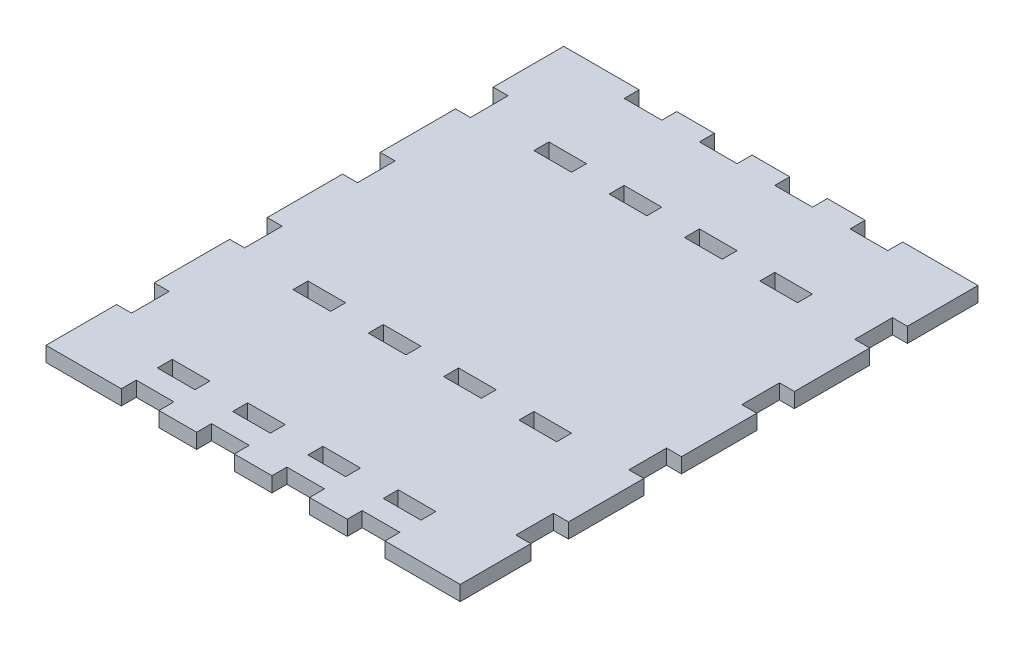
SolidWorks part; units mm, degrees
ref_plane "Front Plane" through (0, 0, 0) normal (0, 0, 1) x (1, 0, 0)
ref_plane "Top Plane" through (0, 0, 0) normal (0, 1, 0) x (1, 0, 0)
ref_plane "Right Plane" through (0, 0, 0) normal (1, 0, 0) x (0, 0, -1)
sketch "Sketch1" plane through (0, 0, 0) normal (0, 1, 0) x (1, 0, 0)
  line L1 (0, 0) -> (88, 0)
  line L2 (0, 0) -> (0, -110)
  line L3 (0, -110) -> (88, -110)
  line L4 (88, 0) -> (88, -110)
  dimension "D1" = 110
  dimension "D2" = 88
extrude "Boss-Extrude1" add sketch "Sketch1" along normal blind 3.175
sketch "Sketch2" plane through (0, 3.175, 0) normal (0, 1, 0) x (1, 0, 0)
  line L0 (44, 0) -> (44, -110) construction
  line L1 (88, 0) -> (0, 0) construction
  line L2 (0, -110) -> (88, -110) construction
  line L3 (64, 0) -> (64, -3.175)
  line L4 (48, 0) -> (56, 0)
  line L5 (48, 0) -> (48, -3.175)
  line L6 (48, -3.175) -> (56, -3.175)
  line L7 (56, 0) -> (56, -3.175)
  line L8 (64, 0) -> (72, 0)
  line L9 (64, -3.175) -> (72, -3.175)
  line L10 (72, 0) -> (72, -3.175)
  line L11 (16, 0) -> (16, -3.175)
  line L12 (24, -3.175) -> (16, -3.175)
  line L13 (24, 0) -> (16, 0)
  line L14 (32, 0) -> (32, -3.175)
  line L15 (40, -3.175) -> (32, -3.175)
  line L16 (40, 0) -> (40, -3.175)
  line L17 (40, 0) -> (32, 0)
  line L18 (24, 0) -> (24, -3.175)
  line L19 (88, -55) -> (0, -55) construction
  line L20 (88, -110) -> (88, 0) construction
  line L21 (0, 0) -> (0, -110) construction
  line L22 (0, -23) -> (3.175, -23)
  line L23 (0, -47) -> (3.175, -47)
  line L24 (0, -47) -> (0, -39)
  line L25 (0, -39) -> (3.175, -39)
  line L26 (3.175, -47) -> (3.175, -39)
  line L27 (0, -23) -> (0, -15)
  line L28 (0, -15) -> (3.175, -15)
  line L29 (3.175, -23) -> (3.175, -15)
  line L30 (3.175, -87) -> (3.175, -95)
  line L31 (0, -95) -> (3.175, -95)
  line L32 (0, -87) -> (0, -95)
  line L33 (3.175, -63) -> (3.175, -71)
  line L34 (0, -71) -> (3.175, -71)
  line L35 (0, -63) -> (0, -71)
  line L36 (0, -63) -> (3.175, -63)
  line L37 (0, -87) -> (3.175, -87)
  line L38 (24, -110) -> (24, -106.825)
  line L39 (40, -110) -> (32, -110)
  line L40 (40, -110) -> (40, -106.825)
  line L41 (40, -106.825) -> (32, -106.825)
  line L42 (32, -110) -> (32, -106.825)
  line L43 (24, -110) -> (16, -110)
  line L44 (24, -106.825) -> (16, -106.825)
  line L45 (16, -110) -> (16, -106.825)
  line L46 (72, -110) -> (72, -106.825)
  line L47 (64, -106.825) -> (72, -106.825)
  line L48 (64, -110) -> (72, -110)
  line L49 (56, -110) -> (56, -106.825)
  line L50 (48, -106.825) -> (56, -106.825)
  line L51 (48, -110) -> (48, -106.825)
  line L52 (48, -110) -> (56, -110)
  line L53 (64, -110) -> (64, -106.825)
  line L54 (88, -87) -> (84.825, -87)
  line L55 (88, -63) -> (84.825, -63)
  line L56 (88, -63) -> (88, -71)
  line L57 (88, -71) -> (84.825, -71)
  line L58 (84.825, -63) -> (84.825, -71)
  line L59 (88, -87) -> (88, -95)
  line L60 (88, -95) -> (84.825, -95)
  line L61 (84.825, -87) -> (84.825, -95)
  line L62 (84.825, -23) -> (84.825, -15)
  line L63 (88, -15) -> (84.825, -15)
  line L64 (88, -23) -> (88, -15)
  line L65 (84.825, -47) -> (84.825, -39)
  line L66 (88, -39) -> (84.825, -39)
  line L67 (88, -47) -> (88, -39)
  line L68 (88, -47) -> (84.825, -47)
  line L69 (88, -23) -> (84.825, -23)
  dimension "D1" = 8
  dimension "D2" = 4
  dimension "D4" = 3.175
  dimension "D5" = 3.175
  dimension "D6" = 8
  dimension "D7" = 8
  dimension "D3" = 2
  dimension "D8" = 2
extrude "Cut-Extrude1" cut sketch "Sketch2" against normal up to next
sketch "Sketch3" plane through (0, 3.175, 0) normal (0, 1, 0) x (1, 0, 0)
  line L0 (0, -19.175) -> (88, -19.175) construction
  line L1 (0, -23) -> (0, -39) construction
  line L2 (88, -39) -> (88, -23) construction
  line L3 (16, -3.175) -> (24, -3.175) construction
  line L4 (44, 0) -> (44, -110) construction
  line L5 (48, 0) -> (40, 0) construction
  line L6 (40, -110) -> (48, -110) construction
  line L7 (64, -19.175) -> (72, -19.175)
  line L8 (48, -19.175) -> (56, -19.175)
  line L9 (48, -19.175) -> (48, -22.35)
  line L10 (48, -22.35) -> (56, -22.35)
  line L11 (56, -19.175) -> (56, -22.35)
  line L12 (64, -19.175) -> (64, -22.35)
  line L13 (64, -22.35) -> (72, -22.35)
  line L14 (72, -19.175) -> (72, -22.35)
  line L15 (16, -19.175) -> (16, -22.35)
  line L16 (24, -22.35) -> (16, -22.35)
  line L17 (24, -19.175) -> (24, -22.35)
  line L18 (32, -19.175) -> (32, -22.35)
  line L19 (40, -22.35) -> (32, -22.35)
  line L20 (40, -19.175) -> (40, -22.35)
  line L21 (40, -19.175) -> (32, -19.175)
  line L22 (24, -19.175) -> (16, -19.175)
  dimension "D1" = 16
  dimension "D2" = 3.175
  dimension "D3" = 8
  dimension "D4" = 4
  dimension "D5" = 2
extrude "Cut-Extrude2" cut sketch "Sketch3" against normal up to next
sketch "Sketch4" plane through (0, 3.175, 0) normal (0, 1, 0) x (1, 0, 0)
  line L0 (0, -73.525) -> (88, -73.525) construction
  line L1 (0, -71) -> (0, -87) construction
  line L2 (88, -87) -> (88, -71) construction
  line L3 (64, -3.175) -> (72, -3.175) construction
  line L4 (44, 0) -> (44, -110) construction
  line L5 (64, -70.35) -> (72, -70.35)
  line L6 (48, -70.35) -> (56, -70.35)
  line L7 (48, -70.35) -> (48, -73.525)
  line L8 (48, -73.525) -> (56, -73.525)
  line L9 (56, -70.35) -> (56, -73.525)
  line L10 (64, -70.35) -> (64, -73.525)
  line L11 (64, -73.525) -> (72, -73.525)
  line L12 (72, -70.35) -> (72, -73.525)
  line L13 (16, -70.35) -> (16, -73.525)
  line L14 (24, -73.525) -> (16, -73.525)
  line L15 (24, -70.35) -> (24, -73.525)
  line L16 (32, -70.35) -> (32, -73.525)
  line L17 (40, -73.525) -> (32, -73.525)
  line L18 (40, -70.35) -> (40, -73.525)
  line L19 (40, -70.35) -> (32, -70.35)
  line L20 (24, -70.35) -> (16, -70.35)
  line L21 (48, 0) -> (40, 0) construction
  line L22 (64, -99.175) -> (72, -99.175)
  line L23 (48, -99.175) -> (56, -99.175)
  line L24 (48, -99.175) -> (48, -102.35)
  line L25 (48, -102.35) -> (56, -102.35)
  line L26 (56, -99.175) -> (56, -102.35)
  line L27 (64, -99.175) -> (64, -102.35)
  line L28 (64, -102.35) -> (72, -102.35)
  line L29 (72, -99.175) -> (72, -102.35)
  line L30 (16, -99.175) -> (16, -102.35)
  line L31 (24, -102.35) -> (16, -102.35)
  line L32 (24, -99.175) -> (24, -102.35)
  line L33 (32, -99.175) -> (32, -102.35)
  line L34 (40, -102.35) -> (32, -102.35)
  line L35 (40, -99.175) -> (40, -102.35)
  line L36 (40, -99.175) -> (32, -99.175)
  line L37 (24, -99.175) -> (16, -99.175)
  line L38 (44, -28.825) -> (44, -138.825) construction
  point P26 (44, -73.525)
  dimension "D1" = 70.35
  dimension "D2" = 3.175
  dimension "D3" = 8
  dimension "D4" = 4
  dimension "D5" = 0
  dimension "D6" = 8
  dimension "D7" = 0
  dimension "D8" = 0
  dimension "D9" = 8
  dimension "D10" = 0
  dimension "D11" = 0
  dimension "D12" = 3.175
  dimension "D13" = 8
  dimension "D15" = 32
  dimension "D14" = 2
extrude "Cut-Extrude3" cut sketch "Sketch4" against normal up to next
